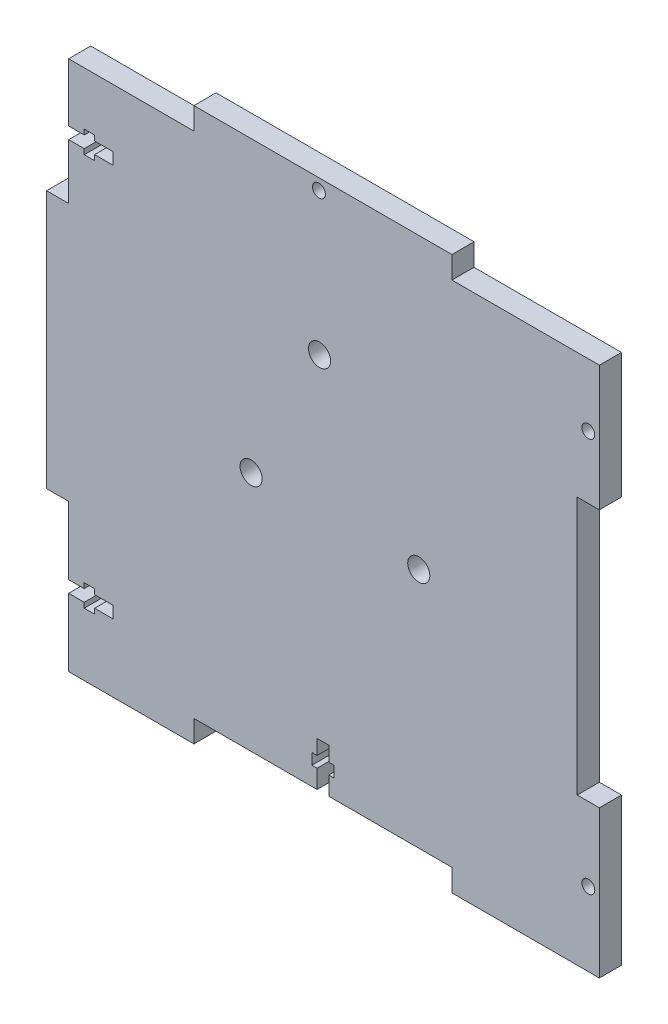
SolidWorks part; units mm, degrees
ref_plane "Front Plane" through (0, 0, 0) normal (0, 0, 1) x (1, 0, 0)
ref_plane "Top Plane" through (0, 0, 0) normal (0, 1, 0) x (1, 0, 0)
ref_plane "Right Plane" through (0, 0, 0) normal (1, 0, 0) x (0, 0, -1)
sketch "Sketch1" plane through (0, 0, 0) normal (0, 0, 1) x (1, 0, 0)
  line L0 (-38, 72) -> (-38, 78)
  line L1 (-72, -72) -> (72, -72)
  line L2 (-72, -72) -> (-72, 72)
  line L3 (-72, 72) -> (72, 72)
  line L4 (72, -72) -> (72, 72)
  line L5 (-72, -72) -> (72, 72) construction
  line L6 (-72, 72) -> (72, -72) construction
  line L7 (-38, 78) -> (32, 78)
  line L8 (32, 78) -> (32, 72)
  line L9 (-38, -72) -> (-38, -66)
  line L10 (-38, -66) -> (32, -66)
  line L11 (32, -66) -> (32, -72)
  line L12 (-72, 38) -> (-78, 38)
  line L13 (-78, 38) -> (-78, -32)
  line L14 (-78, -32) -> (-72, -32)
  line L15 (72, 38) -> (66, 38)
  line L16 (66, 38) -> (66, -32)
  line L17 (66, -32) -> (72, -32)
  line L18 (0, 108.2426) -> (0, -112.6743) construction
  line L19 (-72, 56.2) -> (-60, 56.2)
  line L24 (-72, -50.4) -> (-60, -50.4)
  line L25 (-72, -50.4) -> (-72, -53.6)
  line L26 (-72, -53.6) -> (-60, -53.6)
  line L27 (-60, -50.4) -> (-60, -53.6)
  line L28 (-67.7819, -49) -> (-64.967, -49)
  line L29 (-67.7819, -49) -> (-67.7819, -55)
  line L30 (-67.7819, -55) -> (-64.967, -55)
  line L31 (-64.967, -49) -> (-64.967, -55)
  line L32 (-72, 53) -> (-60, 53)
  line L33 (-60, 56.2) -> (-60, 53)
  line L34 (-67.7728, 57.6) -> (-64.958, 57.6)
  line L35 (-67.7728, 57.6) -> (-67.7728, 51.5685)
  line L36 (-67.7728, 51.5685) -> (-64.958, 51.5685)
  line L37 (-64.958, 57.6) -> (-64.958, 51.5685)
  line L39 (-4.6, -54) -> (-1.4, -54)
  line L40 (-4.6, -54) -> (-4.6, -66)
  line L41 (-4.6, -66) -> (-1.4, -66)
  line L42 (-1.4, -54) -> (-1.4, -66)
  line L43 (-6, -58) -> (0, -58)
  line L44 (-6, -58) -> (-6, -61)
  line L45 (-6, -61) -> (0, -61)
  line L46 (0, -58) -> (0, -61)
  circle A0 centre (69, 55) radius 1.75
  circle A3 centre (69, -52) radius 1.75
  circle A4 centre (-4.09, 75) radius 1.75
  point P0 (0, 0)
  dimension "D16" = 3.5
  dimension "D20" = 12
  dimension "D19" = 3.2
  dimension "D30" = 3
  dimension "D31" = 76.09
  dimension "D2" = 6
  dimension "D3" = 40
  dimension "D4" = 40
  dimension "D5" = 6
  dimension "D6" = 40
  dimension "D7" = 150
  dimension "D8" = 6
  dimension "D9" = 6
  dimension "D10" = 40
  dimension "D11" = 40
  dimension "D12" = 6
  dimension "D13" = 40
  dimension "D14" = 40
  dimension "D15" = 150
  dimension "D17" = 3
  dimension "D18" = 17
  dimension "D21" = 18.4
  dimension "D22" = 3
  dimension "D23" = 6
  dimension "D24" = 20
  dimension "D25" = 1.4
  dimension "D26" = 15
  dimension "D27" = 1.4
  dimension "D28" = 3.2
  dimension "D29" = 12
  dimension "D32" = 40
  dimension "D33" = 3.2
  dimension "D34" = 12
  dimension "D35" = 3
  dimension "D36" = 1.4
  dimension "D37" = 6
  dimension "D38" = 5
  dimension "D39" = 33.4
  dimension "D40" = 0
extrude "Boss-Extrude2" add sketch "Sketch1" along normal blind 6 contours L17 L16 L15 L4 L3 L2 L1 L9 L10 L11 | L13 L14 L2 L12 | L8 L7 L0 L3
sketch "Sketch2" plane through (0, 0, 0) normal (0, 0, -1) x (-1, 0, 0)
  line L0 (4, -0.5) -> (-48, -0.5) construction
  line L1 (-23, -25.5) -> (-23, 24.5) construction
  line L2 (22.5, -20.8841) -> (22.5, 19.8841) construction
  circle A1 centre (3.9247, 36.4917) radius 3
  circle A2 centre (-23, -0.5) radius 3
  circle A3 centre (22.5, -0.5) radius 3
sketch "Sketch3" plane through (0, 0, 0) normal (0, 0, -1) x (-1, 0, 0)
  circle A0 centre (3.9247, 36.4917) radius 3
extrude "Cut-Extrude1" cut sketch "Sketch3" against normal through all
sketch "Sketch4" plane through (0, 0, 0) normal (0, 0, -1) x (-1, 0, 0)
  circle A0 centre (-23, -0.5) radius 3
  circle A1 centre (22.5, -0.5) radius 3
extrude "Cut-Extrude2" cut sketch "Sketch4" against normal through all
equation "\"`2\"=15.927"
